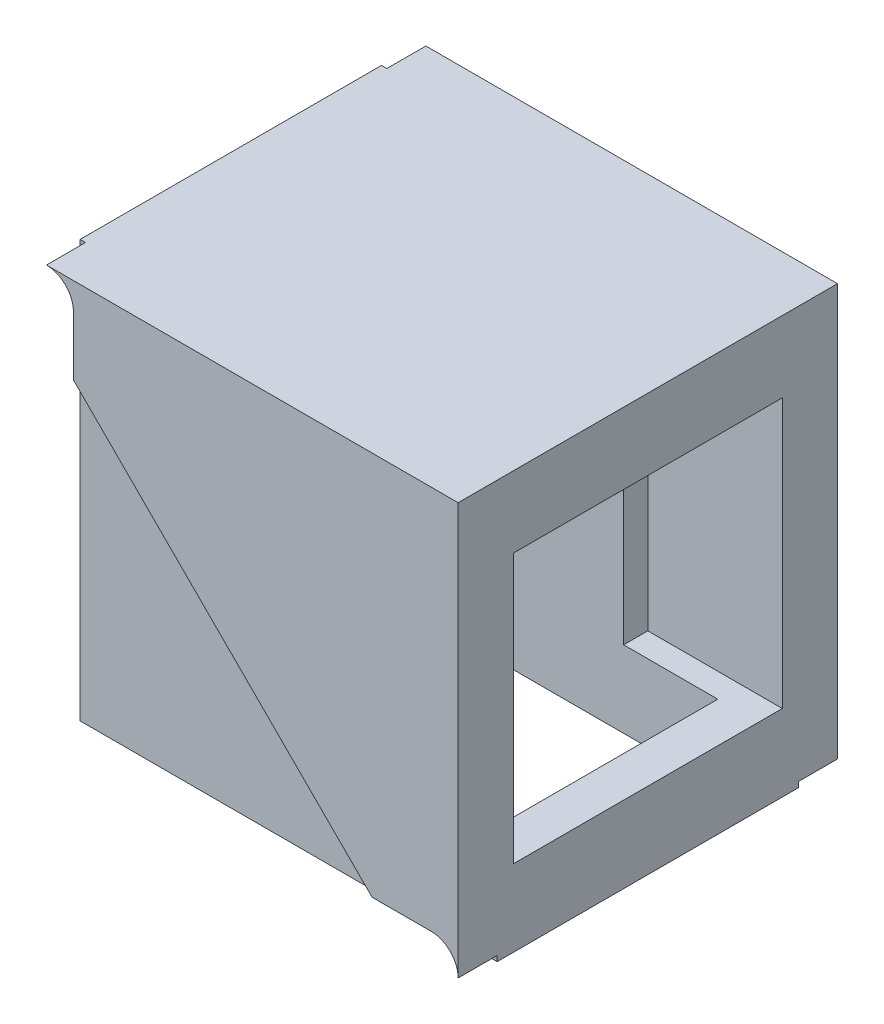
SolidWorks part; units mm, degrees
ref_plane "前视基准面" through (0, 0, 0) normal (0, 0, 1) x (1, 0, 0)
ref_plane "上视基准面" through (0, 0, 0) normal (0, 1, 0) x (1, 0, 0)
ref_plane "右视基准面" through (0, 0, 0) normal (1, 0, 0) x (0, 0, -1)
other "Configuration Table"
ref_plane "基准面1" through (835, 815, -2.8) normal (0, 0, 1) x (-1, 0, 0)
ref_plane "基准面2" through (835, 815, -25.2) normal (0, 0, 1) x (-1, 0, 0)
sketch "草图5" plane through (835, 815, -2.8) normal (0, 0, 1) x (-1, 0, 0)
  line L0 (831, 811) -> (831, 780) construction
  line L1 (800, 811) -> (831, 811) construction
  line L2 (831, 811) -> (831, 780)
  line L3 (800, 811) -> (831, 811)
  line L4 (831, 780) -> (800, 780)
  line L5 (800, 811) -> (800, 780)
extrude "凸台-拉伸1" add sketch "草图5" against normal blind 3
sketch "草图6" plane through (835, 815, -25.2) normal (0, 0, 1) x (-1, 0, 0)
  line L4 (831, 811) -> (800, 811)
  line L5 (831, 780) -> (831, 811)
  line L6 (800, 780) -> (831, 780)
  line L7 (800, 811) -> (800, 780)
  line L8 (831, 811) -> (800, 811)
  line L9 (831, 780) -> (831, 811)
  line L10 (800, 780) -> (831, 780)
  line L11 (800, 811) -> (800, 780)
  dimension "D1" = 0
extrude "凸台-拉伸2" add sketch "草图6" along normal blind 3 separate body
sketch "草图7" plane through (0, 0, -25.2) normal (0, 0, -1) x (-1, 0, 0)
  line L0 (-6.4, 28.6) -> (-28.6, 6.4) construction
  line L1 (-28.6, 6.4) -> (-33, 6.4) construction
  line L2 (-6.4, 28.6) -> (-28.6, 6.4)
  line L3 (-28.6, 6.4) -> (-33, 6.4)
  line L4 (-6.4, 28.6) -> (-6.4, 33) construction
  line L5 (-6.4, 28.6) -> (-6.4, 33)
  line L6 (-35, 4.4) -> (-35, 35)
  line L7 (-35, 35) -> (-4.4, 35)
  arc A0 (-33, 6.4) -> (-35, 4.4) centre (-33, 4.4) ccw construction
  arc A1 (-33, 6.4) -> (-35, 4.4) centre (-33, 4.4) ccw
  arc A2 (-4.4, 35) -> (-6.4, 33) centre (-4.4, 33) ccw construction
  arc A3 (-4.4, 35) -> (-6.4, 33) centre (-4.4, 33) ccw
extrude "凸台-拉伸3" add sketch "草图7" along normal blind 2.9
sketch "草图8" plane through (0, 0, -2.8) normal (0, 0, 1) x (1, 0, 0)
  line L5 (6.4, 33) -> (6.4, 28.6)
  line L6 (35, 35) -> (4.4, 35)
  line L7 (35, 4.4) -> (35, 35)
  line L8 (28.6, 6.4) -> (33, 6.4)
  line L9 (6.4, 28.6) -> (28.6, 6.4)
  line L10 (6.4, 33) -> (6.4, 28.6)
  line L11 (35, 35) -> (4.4, 35)
  line L12 (35, 4.4) -> (35, 35)
  line L13 (28.6, 6.4) -> (33, 6.4)
  line L14 (6.4, 28.6) -> (28.6, 6.4)
  arc A2 (6.4, 33) -> (4.4, 35) centre (4.4, 33) ccw
  arc A3 (35, 4.4) -> (33, 6.4) centre (33, 4.4) ccw
  arc A4 (6.4, 33) -> (4.4, 35) centre (4.4, 33) ccw
  arc A5 (35, 4.4) -> (33, 6.4) centre (33, 4.4) ccw
  dimension "D1" = 0
extrude "凸台-拉伸4" add sketch "草图8" along normal blind 2.9
sketch "草图9" plane through (0, 0, -5.8) normal (0, 0, -1) x (-1, 0, 0)
  line L11 (-35, 4) -> (-32, 4)
  line L12 (-35, 4) -> (-35, 35)
  line L14 (-35, 4) -> (-4, 4)
  line L15 (-4, 4) -> (-4, 35)
  line L16 (-4, 35) -> (-35, 35)
  line L17 (-35, 35) -> (-35, 4)
  line L18 (-35, 4) -> (-4, 4) construction
  line L19 (-4, 4) -> (-4, 35) construction
  line L20 (-4, 35) -> (-35, 35) construction
  line L21 (-35, 35) -> (-35, 4) construction
  line L22 (-32, 4) -> (-32, 32)
  line L23 (-4, 35) -> (-35, 35)
  line L24 (-4, 35) -> (-4, 32)
  line L25 (-4, 32) -> (-32, 32)
  dimension "D1" = 0
  dimension "D2" = 3
  dimension "D3" = 3
extrude "凸台-拉伸5" add sketch "草图9" along normal up to surface (16.4 mm away) up to face at (19.5, 19.5, -22.2)
sketch "草图10" plane through (35, 0, 0) normal (1, 0, 0) x (0, 0, -1)
  line L0 (4, 29.7) -> (4, 9.7)
  line L1 (24, 9.7) -> (4, 9.7)
  line L8 (28.1, 19.7) -> (-0.1, 19.7) construction
  line L9 (14, 4) -> (14, 35) construction
  line L10 (24, 29.7) -> (4, 29.7)
  line L11 (24, 29.7) -> (24, 9.7)
  line L16 (25.2, 4) -> (25.2, 4.4)
  line L17 (25.2, 4.4) -> (28.1, 4.4)
  line L18 (28.1, 4.4) -> (28.1, 35)
  line L19 (28.1, 35) -> (-0.1, 35)
  line L20 (-0.1, 35) -> (-0.1, 4.4)
  line L21 (-0.1, 4.4) -> (2.8, 4.4)
  line L22 (2.8, 4.4) -> (2.8, 4)
  line L23 (2.8, 4) -> (25.2, 4)
  line L24 (25.2, 4) -> (25.2, 4.4) construction
  line L25 (25.2, 4.4) -> (28.1, 4.4) construction
  line L26 (28.1, 4.4) -> (28.1, 35) construction
  line L27 (28.1, 35) -> (-0.1, 35) construction
  line L28 (-0.1, 35) -> (-0.1, 4.4) construction
  line L29 (-0.1, 4.4) -> (2.8, 4.4) construction
  line L30 (2.8, 4.4) -> (2.8, 4) construction
  line L31 (2.8, 4) -> (25.2, 4) construction
  dimension "D2" = 10
  dimension "D3" = 20
  dimension "D4" = 20
  dimension "D5" = 10
  dimension "D1" = 0
extrude "切除-拉伸1" cut sketch "草图10" against normal blind 10
